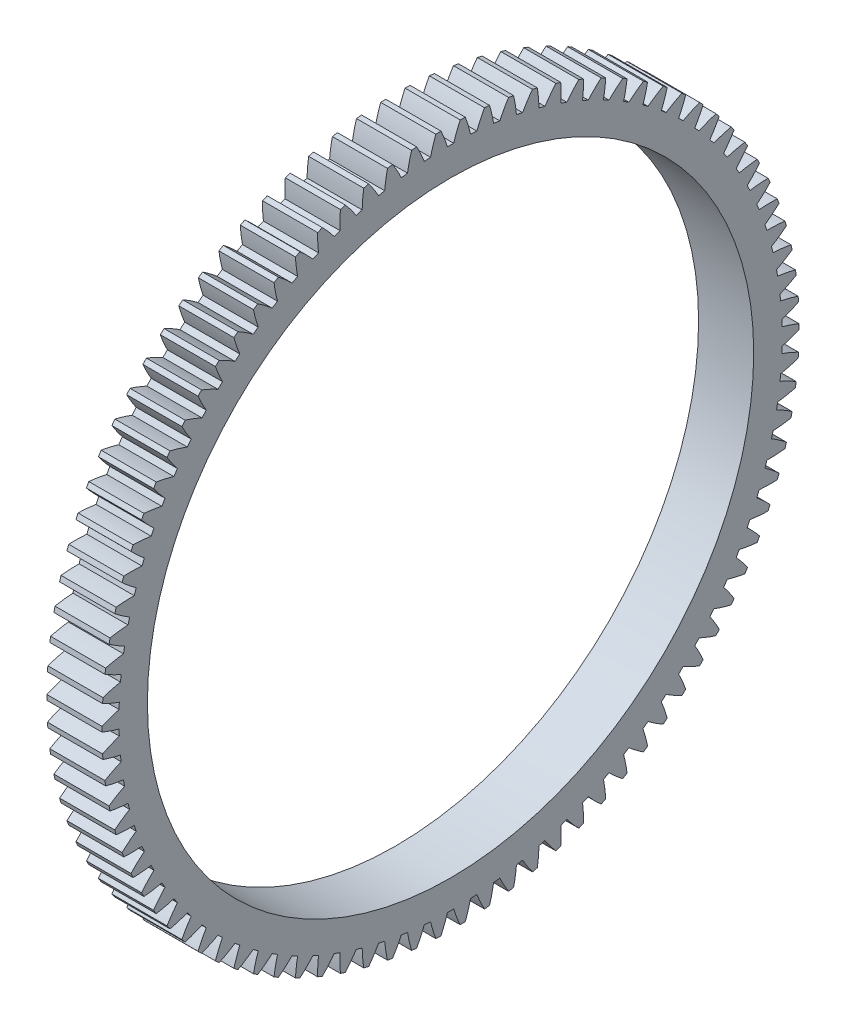
SolidWorks part; units mm, degrees
ref_plane "Plane1" through (0, 0, 0) normal (0, 0, 1) x (1, 0, 0)
ref_plane "Plane2" through (0, 0, 0) normal (0, 1, 0) x (1, 0, 0)
ref_plane "Plane3" through (0, 0, 0) normal (1, 0, 0) x (0, 0, -1)
sketch "HoldingSke" plane through (0, 0, 0) normal (0, 1, 0) x (1, 0, 0)
  line L0 (0, 0) -> (0, -0.7273)
  line L1 (-15, 0) -> (100, 0) construction
  line L2 (0, 0) -> (-2.1039, 2.3779)
  line L3 (0, 0) -> (-11.863, 4.5341)
  line L4 (0, 0) -> (0, 8.636)
  line L5 (0, 0) -> (-46.8476, -17.4728)
  line L6 (0, 0) -> (-8.2896, -5.593)
  line L7 (-2.1039, 2.3779) -> (8.6586, 51.2059)
  line L8 (-76.2, 54.61) -> (-68.8, 54.61)
  line L9 (-71.009, 38.7566) -> (-53.1078, 45.2721)
  line L10 (-76.2, 71.12) -> (104.1128, 71.12)
  line L11 (0, 0) -> (-10, 0)
  line L12 (-76.2, 101.6) -> (-76.151, 101.6)
  line L13 (24.9733, 27.94) -> (52.9518, 28.4284)
  line L14 (24.9733, 27.94) -> (24.9743, 27.94)
  line L15 (24.9733, 27.94) -> (100.4006, 29.5858)
  line L16 (-63.627, -1.375) -> (-12.827, -1.375)
  circle A0 centre (0, 0) radius 55
  circle A1 centre (0, 0) radius 37.5
  circle A2 centre (0, 0) radius 37.5
  circle A3 centre (0, 0) radius 55
  dimension "MHD" = 75
  dimension "Hub_dia" = 75
  dimension "Bore" = 110
  dimension "MBD" = 110
  dimension "Num_teeth" = 90
  dimension "Pitch" = 0.7273
  dimension "Overall_len" = 50
  dimension "Show_teeth" = 90
  dimension "Thickness" = 10
  dimension "OAL" = 50.0001
  dimension "T_dim" = 7.4
  dimension "Ap" = 20
  dimension "H" = 19.05
  dimension "Pitch_radius" = 180.3128
  dimension "Width" = 10
  dimension "Backlash" = 0.049
  dimension "Addendum_fac" = 1
  dimension "Dedendum_fac" = 1.25
  dimension "Clearance_fac" = 0.25
  dimension "Dedendum_add" = 0.001
  dimension "Module" = 1.375
sketch "BasProSke" plane through (0, 0, 0) normal (0, 1, 0) x (1, 0, 0)
  line L0 (-10, 0) -> (60, 0) construction
  line L1 (0, 0) -> (0, 63.25)
  line L2 (0, 0) -> (10, 0)
  line L3 (10, 0) -> (10, 63.25)
  line L4 (10, 63.25) -> (0, 63.25)
  dimension "Thickness" = 10
  dimension "Diameter" = 126.5
revolve "Base-Revolve" add sketch "BasProSke" angle 360 about L0
sketch "TooCutSke" plane through (0, 0, 0) normal (1, 0, 0) x (0, 0, -1)
  line L1 (0, 0) -> (0, 107) construction
  line L2 (0, 0) -> (-1.1656, 61.864) construction
  line L3 (0, 0) -> (-4.3183, 123.6587) construction
  line L4 (-1.1656, 61.864) -> (-2.1591, 61.8293) construction
  arc A0 (0.5684, 60.1526) -> (-0.5684, 60.1526) centre (0, 0) ccw
  arc A1 (1.7567, 63.251) -> (-1.7567, 63.251) centre (0, 0) ccw
  circle A2 centre (0, 0) radius 61.875 construction
  circle A3 centre (0, 0) radius 58.1435 construction
  arc A4 (-0.5684, 60.1526) -> (-1.7567, 63.251) centre (-24.2193, 52.8591) ccw
  arc A5 (1.7567, 63.251) -> (0.5684, 60.1526) centre (24.2193, 52.8591) ccw
  dimension "Root_dia" = 120.3105
  dimension "Overcut_dia" = 126.5508
  dimension "Pitch_dia" = 123.75
  dimension "Base_dia" = 116.287
  dimension "Flank_rad" = 24.75
  dimension "Half_ang" = 2
  dimension "Half_CT" = 0.9941
extrude "ToothCut" cut sketch "TooCutSke" along normal through all
fillet "Breaks" [suppressed] radius 0.0275
fillet "RootFillets" [suppressed] radius 0.3448
pattern_circular "TeethCuts" count 90 every 4 about axis through (-10, 0, 0) along (1, 0, 0) of "ToothCut", "RootFillets", "Breaks"
sketch "HubNeaOneSke" plane through (0, 0, 0) normal (-1, 0, 0) x (0, 0, 1)
  circle A0 centre (0, 0) radius 37.5
  dimension "Diameter" = 75
extrude "HubNearOne" add sketch "HubNeaOneSke" along normal blind 40.0001
sketch "HubNeaBotSke" plane through (0, 0, 0) normal (-1, 0, 0) x (0, 0, 1)
  circle A0 centre (0, 0) radius 37.5
  dimension "Diameter" = 75
extrude "HubNearBoth" [suppressed] add sketch "HubNeaBotSke" along normal blind 20
ref_plane "FarPln" through (10, 0, 0) normal (1, 0, 0) x (0, 0, -1)
sketch "HubFarSke" plane through (10, 0, 0) normal (1, 0, 0) x (0, 0, -1)
  circle A0 centre (0, 0) radius 37.5
  dimension "Diameter" = 75
extrude "HubFar" [suppressed] add sketch "HubFarSke" along normal blind 20
sketch "BorSke" plane through (0, 0, 0) normal (1, 0, 0) x (0, 0, -1)
  circle A0 centre (0, 0) radius 55
  dimension "Diameter" = 110
extrude "Bore" cut sketch "BorSke" along normal mid plane 100.0001
sketch "KeySke" plane through (0, 0, 0) normal (1, 0, 0) x (0, 0, -1)
  line L0 (-16, 0) -> (-16, 62.4)
  line L1 (-16, 62.4) -> (16, 62.4)
  line L2 (16, 62.4) -> (16, 0)
  line L3 (0, 0) -> (0, 34) construction
  line L4 (-16, 0) -> (16, 0)
  dimension "Offset" = 62.4
  dimension "Width" = 32
extrude "Keyway" [suppressed] cut sketch "KeySke" along normal mid plane 100.0001
pattern_circular "Keyway2" [suppressed] count 2 every 90 about axis through (-10, 0, 0) along (1, 0, 0)
equation "' \"Module@HoldingSke\" = 6.35"
equation "' \"Num_teeth@HoldingSke\" = 12"
equation "' \"Ap@HoldingSke\" =  20"
equation "' \"Ap@HoldingSke\" = 20"
equation "' \"Width@HoldingSke\" = 0.5 * 25.4"
equation "' \"Hub_dia@HoldingSke\"= 1 * 25.4"
equation "' \"Hub_dia@HoldingSke\" = 1 * 25.4"
equation "' \"Overall_len@HoldingSke\" = 1.0 * 25.4"
equation "' \"Bore@HoldingSke\" = 0.75 * 25.4"
equation "' \"T_dim@HoldingSke\" = 0.1 * 25.4"
equation "' \"Width@KeySke\" = 0.25 * 25.4"
equation "' \"Show_teeth@HoldingSke\" = 13"
equation "' \"Backlash@HoldingSke\" = 0.009 * 25.4"
equation "' \"Addendum_fac@HoldingSke\" = 1.0"
equation "' \"Dedendum_fac@HoldingSke\" = 1.25"
equation "' \"Dedendum_add@HoldingSke\" = 0.00005 * 25.4"
equation "' \"Clearance_fac@HoldingSke\" = 0.25"
equation "\"Pitch@HoldingSke\" = 1 / \"Module@HoldingSke\""
equation "\"Overcut_dia@TooCutSke\" = (\"Num_teeth@HoldingSke\" + 2 * \"Addendum_fac@HoldingSke\") / \"Pitch@HoldingSke\" + 0.002 * 25.4"
equation "\"Pitch_dia@TooCutSke\" = \"Num_teeth@HoldingSke\" / \"Pitch@HoldingSke\""
equation "\"Base_dia@TooCutSke\" = \"Num_teeth@HoldingSke\" / \"Pitch@HoldingSke\" * cos((\"Ap@HoldingSke\"  * 3.14159265 / 180))"
equation "\"Root_dia@TooCutSke\" = (\"Num_teeth@HoldingSke\" + 2) / \"Pitch@HoldingSke\" - 2 * (\"Addendum_fac@HoldingSke\" + \"Dedendum_fac@HoldingSke\") / \"Pitch@HoldingSke\" - \"Dedendum_add@HoldingSke\" * 2"
equation "\"Half_ang@TooCutSke\" = 180 / \"Num_teeth@HoldingSke\""
equation "\"Half_CT@TooCutSke\" = \"Num_teeth@HoldingSke\" / \"Pitch@HoldingSke\" * sin((3.14159265 / 2 / \"Num_teeth@HoldingSke\")) / 2 - 7 * \"Backlash@HoldingSke\" / 4"
equation "\"Flank_rad@TooCutSke\" = \"Num_teeth@HoldingSke\" / \"Pitch@HoldingSke\" / 5"
equation "\"Radius@RootFillets\" = \"Clearance_fac@HoldingSke\" / \"Pitch@HoldingSke\" + \"Dedendum_add@HoldingSke\""
equation "\"Break_rad@Breaks\" = 0.02 / \"Pitch@HoldingSke\""
equation "\"Thickness@HoldingSke\" = \"Width@HoldingSke\""
equation "\"OAL@HoldingSke\" = \"Thickness@HoldingSke\""
equation "\"MHD@HoldingSke\" = (\"Num_teeth@HoldingSke\" + 2) / \"Pitch@HoldingSke\" - 2 * (\"Addendum_fac@HoldingSke\" + \"Dedendum_fac@HoldingSke\")  / \"Pitch@HoldingSke\" - \"Dedendum_add@HoldingSke\" * 2"
equation "\"MBD@HoldingSke\" = (\"Num_teeth@HoldingSke\" + 2) / \"Pitch@HoldingSke\" - 2 * (\"Addendum_fac@HoldingSke\" + \"Dedendum_fac@HoldingSke\")  / \"Pitch@HoldingSke\" - \"Dedendum_add@HoldingSke\" * 2 - 0.002 * 25.4"
equation "\"MHD@HoldingSke\" = ((sgn( \"MHD@HoldingSke\" - \"Hub_dia@HoldingSke\" )-1)*( \"MHD@HoldingSke\" - \"Hub_dia@HoldingSke\" ))/-2+ \"Hub_dia@HoldingSke\""
equation "\"MBD@HoldingSke\" = ((sgn( \"MBD@HoldingSke\" - \"Bore@HoldingSke\" )-1)*( \"MBD@HoldingSke\" - \"Bore@HoldingSke\" ))/-2+ \"Bore@HoldingSke\""
equation "\"OAL@HoldingSke\" = ((sgn( \"OAL@HoldingSke\" - \"Overall_len@HoldingSke\" )+1)*( \"OAL@HoldingSke\" - \"Overall_len@HoldingSke\" ))/2 + \"Overall_len@HoldingSke\" + 0.000002 * 25.4"
equation "\"Num_teeth@TeethCuts\" = int( \"Show_teeth@HoldingSke\" ) + 1"
equation "\"Num_teeth@TeethCuts\" = ((sgn( \"Num_teeth@TeethCuts\" - \"Num_teeth@HoldingSke\" )-1)*( \"Num_teeth@TeethCuts\" - \"Num_teeth@HoldingSke\" ))/-2+ \"Num_teeth@HoldingSke\""
equation "\"Num_teeth@TeethCuts\" = ((sgn( \"Num_teeth@TeethCuts\" - 2.0)+1)*( \"Num_teeth@TeethCuts\" - 2.0))/2 +2.0"
equation "\"Angle@TeethCuts\" = 360.0 / \"Num_teeth@HoldingSke\""
equation "\"Diameter@BasProSke\" = (\"Num_teeth@HoldingSke\" + 2 * \"Addendum_fac@HoldingSke\") / \"Pitch@HoldingSke\""
equation "\"Thickness@BasProSke\"  = \"Thickness@HoldingSke\""
equation "' \"Fillet_rad@BasProSke\" =  \"Thickness@HoldingSke\" * 0.05"
equation "' \"Fillet_rad@BasProSke\" = \"Thickness@HoldingSke\" * 0.05"
equation "\"MHD@HoldingSke\" = ((sgn( \"MHD@HoldingSke\" - \"Root_dia@TooCutSke\" )-1)*( \"MHD@HoldingSke\" - \"Root_dia@TooCutSke\" ))/-2+ \"Root_dia@TooCutSke\""
equation "\"Diameter@HubNeaOneSke\" = \"MHD@HoldingSke\""
equation "\"Length@HubNearOne\" = \"OAL@HoldingSke\" - \"Thickness@BasProSke\""
equation "\"Diameter@HubNeaBotSke\" = \"MHD@HoldingSke\""
equation "\"Length@HubNearBoth\" = ( \"OAL@HoldingSke\" - \"Thickness@BasProSke\" ) / 2.0"
equation "\"Thickness@FarPln\" = \"Thickness@BasProSke\""
equation "\"Diameter@HubFarSke\" = \"MHD@HoldingSke\""
equation "\"Length@HubFar\" = ( \"OAL@HoldingSke\" - \"Thickness@BasProSke\" ) / 2.0"
equation "\"Diameter@BorSke\" = \"MBD@HoldingSke\""
equation "\"D1@Bore\" = \"OAL@HoldingSke\" * 2.0"
equation "\"D1@Keyway\" = \"OAL@HoldingSke\" * 2.0"
equation "\"Offset@KeySke\" = \"T_dim@HoldingSke\" + \"MBD@HoldingSke\" / 2.0"
